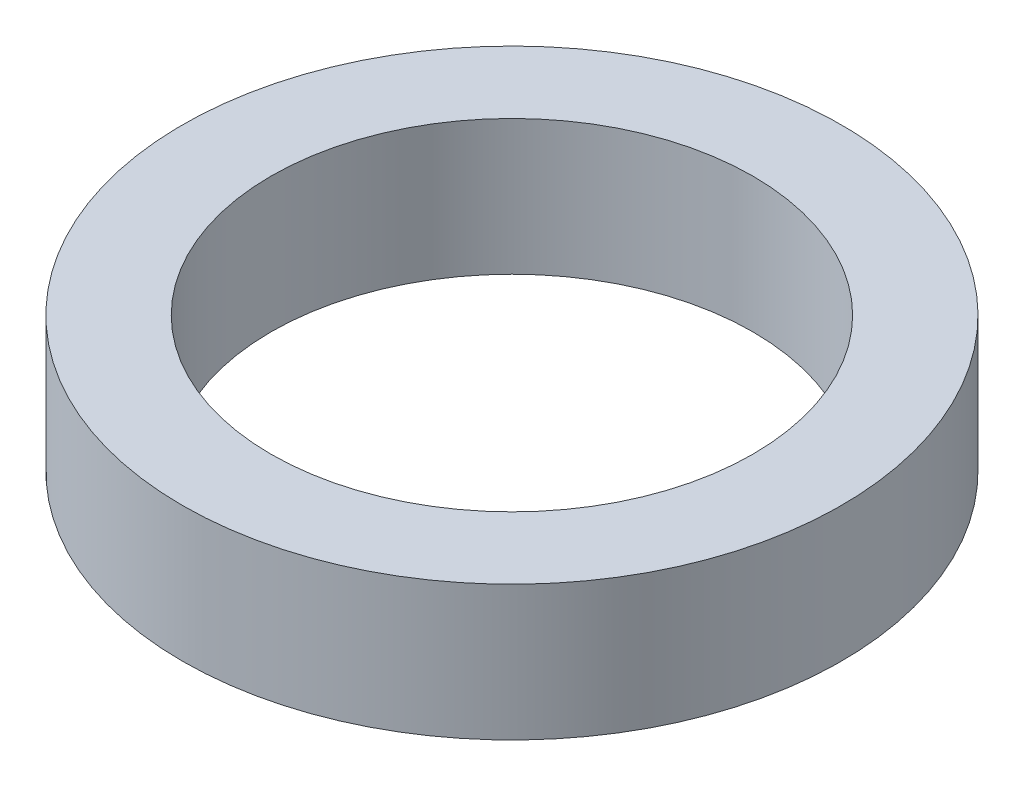
SolidWorks part; units mm, degrees
ref_plane "Front Plane" through (0, 0, 0) normal (0, 0, 1) x (1, 0, 0)
ref_plane "Top Plane" through (0, 0, 0) normal (0, 1, 0) x (1, 0, 0)
ref_plane "Right Plane" through (0, 0, 0) normal (1, 0, 0) x (0, 0, -1)
sketch "Sketch1" plane through (0, 0, 0) normal (0, 1, 0) x (1, 0, 0)
  circle A0 centre (0, 0) radius 12.5
  circle A1 centre (0, 0) radius 17.1
extrude "Boss-Extrude1" add sketch "Sketch1" along normal blind 7 contours A0 | A1
